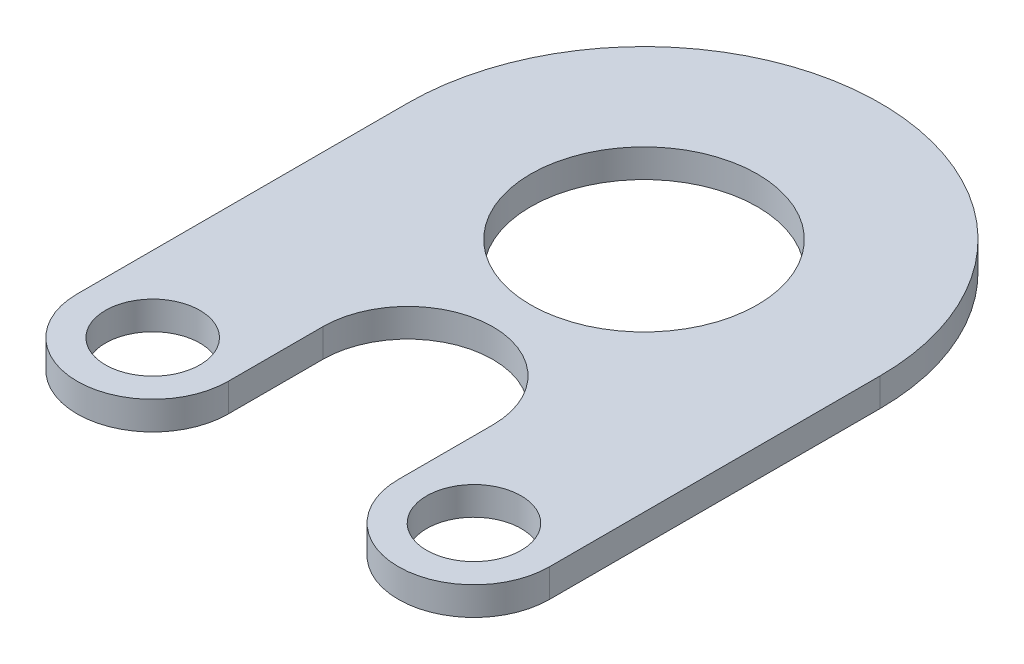
SolidWorks part; units mm, degrees
material "6063-O"
ref_plane "Front Plane" through (0, 0, 0) normal (0, 0, 1) x (1, 0, 0)
ref_plane "Top Plane" through (0, 0, 0) normal (0, 1, 0) x (1, 0, 0)
ref_plane "Right Plane" through (0, 0, 0) normal (1, 0, 0) x (0, 0, -1)
sketch "Sketch1" plane through (0, 0, 0) normal (0, 1, 0) x (1, 0, 0)
  line L0 (-25, 0) -> (-25, -35)
  line L1 (25, 0) -> (25, -35)
  line L2 (9, -35) -> (9, -25)
  line L3 (-9, -25) -> (-9, -35)
  arc A0 (25, 0) -> (-25, 0) centre (0, 0) ccw
  arc A1 (-25, -35) -> (-9, -35) centre (-17, -35) ccw
  arc A2 (9, -35) -> (25, -35) centre (17, -35) ccw
  arc A3 (9, -25) -> (-9, -25) centre (0, -25) ccw
  circle A4 centre (0, 0) radius 12
  circle A5 centre (17, -35) radius 5
  circle A6 centre (-17, -35) radius 5
  dimension "D1" = 24
  dimension "D2" = 25
  dimension "D3" = 35
  dimension "D4" = 8
  dimension "D6" = 10
  dimension "D7" = 10
  dimension "D8" = 10
  dimension "D5" = 8
extrude "Boss-Extrude2" add sketch "Sketch1" along normal mid plane 3
